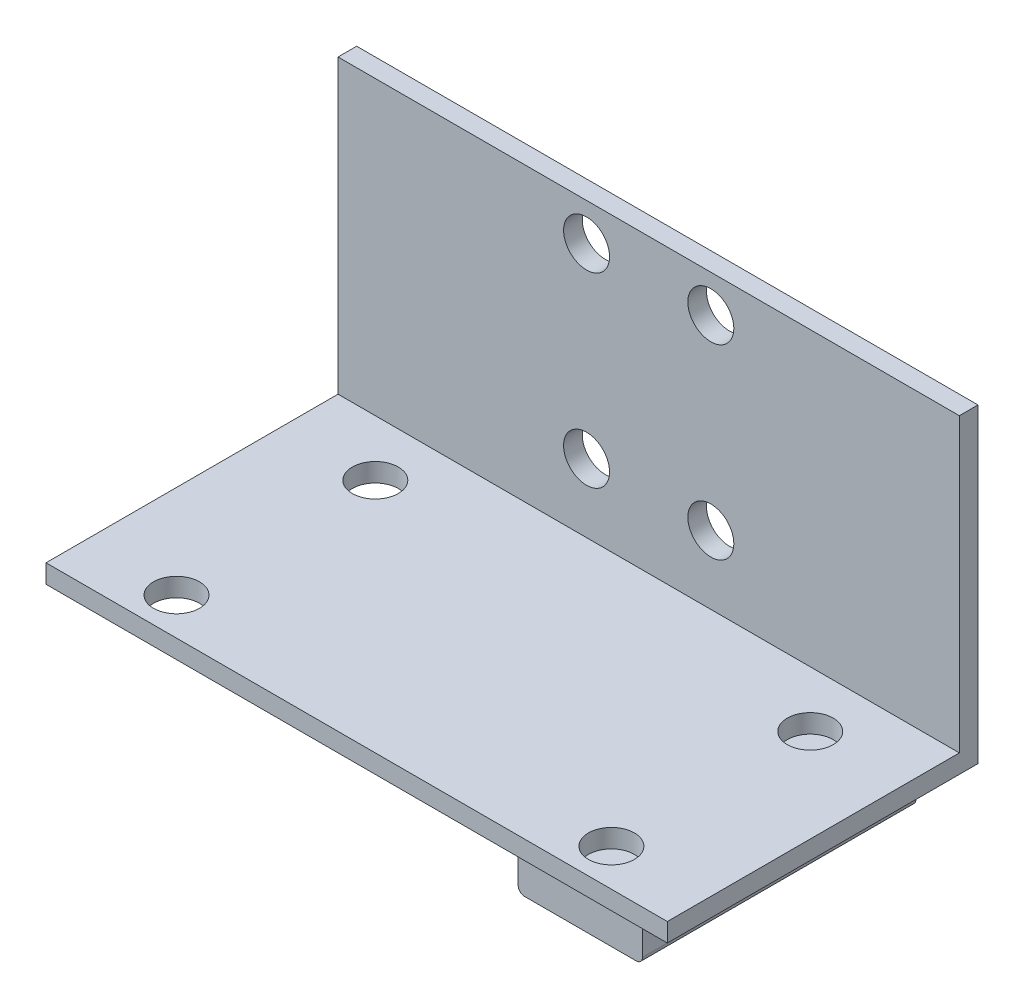
SolidWorks part; units mm, degrees
ref_plane "Front Plane" through (0, 0, 0) normal (0, 0, 1) x (1, 0, 0)
ref_plane "Top Plane" through (0, 0, 0) normal (0, 1, 0) x (1, 0, 0)
ref_plane "Right Plane" through (0, 0, 0) normal (1, 0, 0) x (0, 0, -1)
sketch "Sketch1" plane through (0, 0, 0) normal (0, 1, 0) x (1, 0, 0)
  line L1 (0, 0) -> (50, 0)
  line L2 (0, 0) -> (0, 25)
  line L3 (0, 25) -> (50, 25)
  line L4 (50, 0) -> (50, 25)
  dimension "D1" = 50
  dimension "D2" = 25
extrude "Boss-Extrude1" add sketch "Sketch1" along normal blind 1.5
sketch "Sketch3" plane through (0, 1.5, 0) normal (0, 1, 0) x (1, 0, 0)
  line L0 (50, 25) -> (0, 25) construction
  line L1 (0, 25) -> (50, 25)
  line L2 (0, 25) -> (0, 23.5)
  line L3 (0, 23.5) -> (50, 23.5)
  line L4 (50, 25) -> (50, 23.5)
  line L5 (50, 0) -> (50, 25) construction
  dimension "D1" = 1.5
extrude "Boss-Extrude2" add sketch "Sketch3" along normal blind 23.5
sketch "Sketch4" plane through (0, 0, -23.5) normal (0, 0, 1) x (1, 0, 0)
  line L0 (25, 25) -> (25, 1.5) construction
  line L1 (0, 25) -> (50, 25) construction
  line L2 (0, 1.5) -> (50, 1.5) construction
  circle A0 centre (20, 22) radius 1.85
  circle A1 centre (30, 22) radius 1.85
  circle A2 centre (30, 7) radius 1.85
  circle A3 centre (20, 7) radius 1.85
  dimension "D1" = 3.7
  dimension "D2" = 3.7
  dimension "D3" = 3.7
  dimension "D4" = 3.7
  dimension "D5" = 15
  dimension "D6" = 10
  dimension "D7" = 3
extrude "Cut-Extrude1" cut sketch "Sketch4" against normal blind 23
sketch "Sketch5" plane through (0, 1.5, 0) normal (0, 1, 0) x (1, 0, 0)
  line L0 (0, 0) -> (50, 0) construction
  line L1 (25, 23.5) -> (25, 0) construction
  line L2 (0, 23.5) -> (50, 23.5) construction
  circle A0 centre (7.5, 3) radius 1.85
  circle A1 centre (7.5, 19) radius 1.85
  circle A2 centre (42.5, 3) radius 1.85
  circle A3 centre (42.5, 19) radius 1.85
  dimension "D1" = 3.7
  dimension "D2" = 3.7
  dimension "D3" = 3.7
  dimension "D4" = 3.7
  dimension "D5" = 16
  dimension "D6" = 3
  dimension "D7" = 35
extrude "Cut-Extrude2" cut sketch "Sketch5" against normal blind 23
sketch "Sketch6" plane through (0, 0, 0) normal (0, -1, 0) x (1, 0, 0)
  line L0 (42.5, -20.85) -> (42.5, -12.2066) construction
  line L1 (47.5, -22.5) -> (37.5, -22.5)
  line L2 (47.5, -22.5) -> (47.5, -0.5)
  line L3 (47.5, -0.5) -> (37.5, -0.5)
  line L4 (37.5, -22.5) -> (37.5, -0.5)
  line L7 (50, -25) -> (0, -25) construction
  circle A0 centre (42.5, -19) radius 1.85 construction
  dimension "D1" = 10
  dimension "D2" = 22
  dimension "D3" = 2.5
extrude "Boss-Extrude3" add sketch "Sketch6" along normal blind 3
fillet "Fillet1" radius 0.5 2 edges at (47.5, -3, -11.5) (37.5, -3, -11.5)
